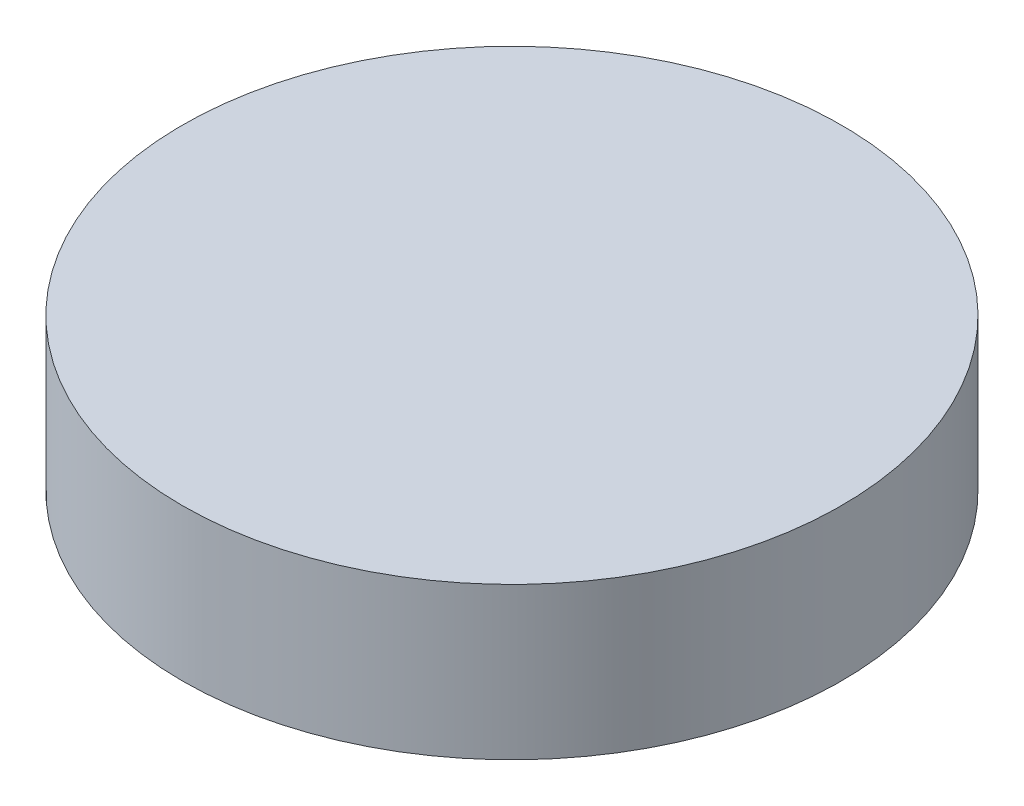
SolidWorks part; units mm, degrees
ref_plane "Front Plane" through (0, 0, 0) normal (0, 0, 1) x (1, 0, 0)
ref_plane "Top Plane" through (0, 0, 0) normal (0, 1, 0) x (1, 0, 0)
ref_plane "Right Plane" through (0, 0, 0) normal (1, 0, 0) x (0, 0, -1)
sketch "Sketch2" plane through (0, 53, 0) normal (0, 1, 0) x (1, 0, 0)
  circle A0 centre (-27.5, 11.5) radius 5.425
  circle A2 centre (-27.5, 11.5) radius 5.675 construction
  circle A4 centre (-27.5, 11.5) radius 5.675 construction
  point P4 (-27.25, 13.5)
  dimension "D1" = 0.25
extrude "Boss-Extrude1" add sketch "Sketch2" against normal offset from surface (2.5 mm away) 0.5
